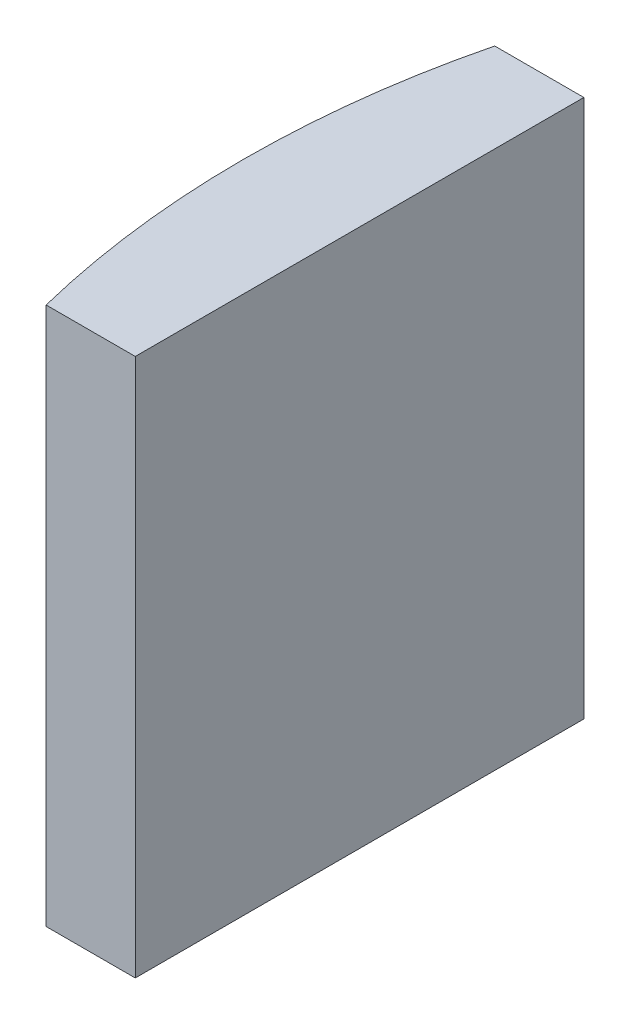
SolidWorks part; units mm, degrees
ref_plane "前视基准面" through (0, 0, 0) normal (0, 0, 1) x (1, 0, 0)
ref_plane "上视基准面" through (0, 0, 0) normal (0, 1, 0) x (1, 0, 0)
ref_plane "右视基准面" through (0, 0, 0) normal (1, 0, 0) x (0, 0, -1)
sketch "草图1" plane through (0, 0, 0) normal (0, 1, 0) x (1, 0, 0)
  line L0 (10.7432, 0) -> (-19.1624, 0) construction
  line L1 (-15.7112, 5) -> (-13.7248, 5)
  line L2 (-15.7112, -5) -> (-13.7248, -5)
  line L3 (-13.7248, 5) -> (-13.7248, -5)
  arc A0 (-15.7112, 5) -> (-15.7112, -5) centre (4.3552, 0) ccw
  point P2 (-19.1624, 0)
  point P19 (-16.3248, 0)
  point P20 (-13.7248, 0)
  dimension "D2" = 5
  dimension "D3" = 20.68
  dimension "D4" = 2.6
  dimension "D1" = 5
extrude "凸台-拉伸1" add sketch "草图1" along normal blind 12
